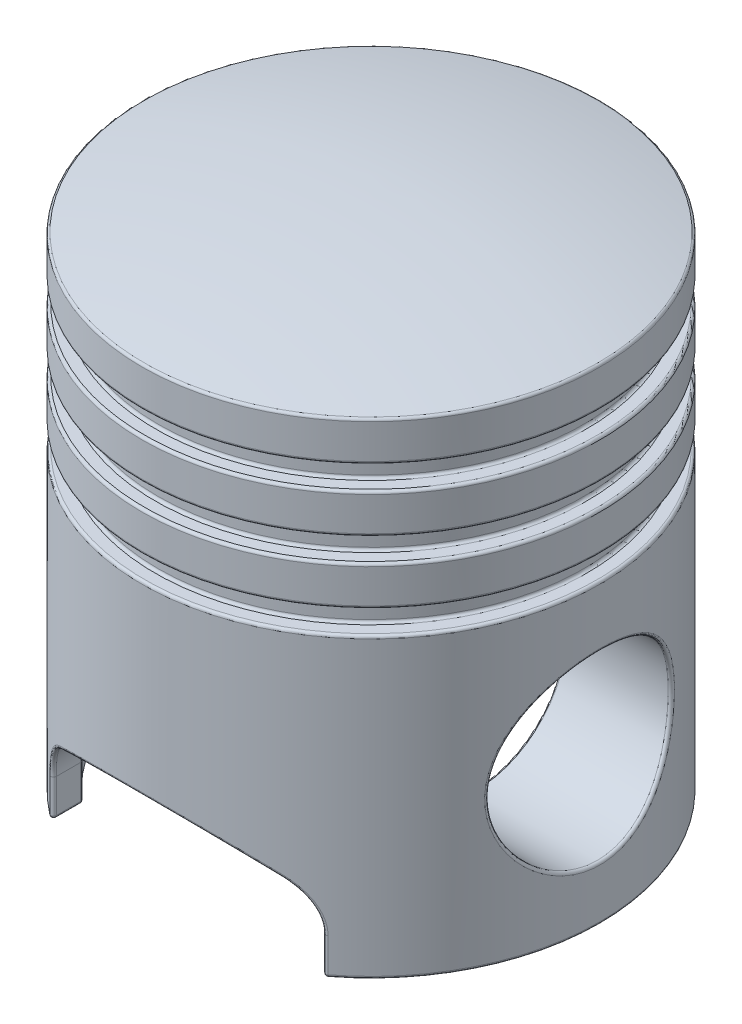
SolidWorks part; units mm, degrees
ref_plane "Front Plane" through (0, 0, 0) normal (0, 0, 1) x (1, 0, 0)
ref_plane "Top Plane" through (0, 0, 0) normal (0, 1, 0) x (1, 0, 0)
ref_plane "Right Plane" through (0, 0, 0) normal (1, 0, 0) x (0, 0, -1)
sketch "Sketch1" plane through (0, 0, 0) normal (0, 0, 1) x (1, 0, 0)
  line L0 (0, 0) -> (0, -76008.205) construction
  line L1 (0, 0) -> (76008.205, 0) construction
  line L2 (0, 95) -> (0, 85)
  line L3 (0, 85) -> (38, 85)
  line L4 (38, 85) -> (38, 0)
  line L5 (38, 0) -> (42.5, 0)
  line L6 (42.5, 0) -> (42.5, 55.2)
  line L7 (42.5, 55.2) -> (39.5, 55.2)
  line L8 (39.5, 55.2) -> (39.5, 59.5)
  line L9 (39.5, 59.5) -> (42.5, 59.5)
  line L10 (42.5, 59.5) -> (42.5, 66.8)
  line L11 (42.5, 66.8) -> (39.5, 66.8)
  line L12 (39.5, 66.8) -> (39.5, 71.1)
  line L13 (39.5, 71.1) -> (42.5, 71.1)
  line L14 (42.5, 71.1) -> (42.5, 78.4)
  line L15 (42.5, 78.4) -> (39.5, 78.4)
  line L16 (39.5, 78.4) -> (39.5, 82.7)
  line L17 (39.5, 82.7) -> (42.5, 82.7)
  line L18 (42.5, 82.7) -> (42.5, 90)
  arc A0 (0, 95) -> (42.5, 90) centre (0, -88.125) cw
  point P7 (0, 0)
  point P24 (5.7863, 67.9402)
  point P26 (61.7259, 86.9589)
  dimension "D1" = 85
  dimension "D2" = 5
  dimension "D3" = 79
  dimension "D4" = 76
  dimension "D5" = 7.3
  dimension "D6" = 4.3
  dimension "D7" = 90
  dimension "D8" = 85
revolve "Revolve1" add sketch "Sketch1" angle 360 about L0
sketch "Sketch2" plane through (0, 0, 0) normal (1, 0, 0) x (0, 0, -1)
  circle A0 centre (0, 27) radius 22.5
  dimension "D1" = 45
  dimension "D2" = 27
extrude "Boss-Extrude1" add sketch "Sketch2" along normal up to next from offset 19
mirror "Mirror1" about plane through (0, 0, 0) normal (1, 0, 0) of "Boss-Extrude1"
sketch "Sketch3" plane through (0, 0, 0) normal (1, 0, 0) x (0, 0, -1)
  circle A0 centre (0, 27) radius 16.9
  dimension "D2" = 33.8
  dimension "D1" = 27
extrude "Cut-Extrude1" cut sketch "Sketch3" against normal through all both and the other way through all
sketch "Sketch4" plane through (0, 0, 0) normal (0, 0, 1) x (1, 0, 0)
  line L0 (0, 0) -> (0, -50000) construction
  line L1 (-25, 0) -> (-25, 12)
  line L2 (-42.5, 0) -> (42.5, 0) construction
  line L3 (25, 0) -> (25, 12)
  line L4 (-25, 0) -> (25, 0)
  arc A0 (-25, 12) -> (25, 12) centre (0, -19.225) cw
  point P10 (0, 0)
  dimension "D2" = 40
  dimension "D1" = 50
  dimension "D3" = 12
extrude "Cut-Extrude2" cut sketch "Sketch4" against normal blind 30 from offset 25 offset against normal yes
fillet "Fillet1" radius 10 2 edges at (25, 12, -31.4937) (-25, 12, -31.4937)
mirror "Mirror2" about plane through (0, 0, 0) normal (0, 0, 1) of "Cut-Extrude2", "Fillet1"
fillet "Fillet2" radius 0.5 50 edges at (-23.3798, 12.2128, 35.4913) (-24.3258, 10.3653, 29.1934) (22.703, 13.1326, 35.928) (23.5198, 11.9916, 29.8466) (3.5136, 20.6204, 42.3545) (25, 0, 31.4937) (-25, 0, 31.4937) (-22.703, 13.1326, -35.928) (-23.5198, 11.9916, -29.8466) (23.3798, 12.2128, -35.4913) (24.3258, 10.3653, -29.1934) (3.5136, 20.6204, -42.3545) (-25, 0, -31.4937) (25, 0, -31.4937) (30.6228, 26.906, -22.4998) (0, 90, 42.5) (0, 82.7, 42.5) (0, 82.7, 39.5) (0, 78.4, 39.5) (0, 78.4, 42.5) (0, 71.1, 42.5) (0, 71.1, 39.5) (0, 66.8, 39.5) (0, 66.8, 42.5) (0, 59.5, 42.5) (0, 59.5, 39.5) (0, 55.2, 39.5) (0, 55.2, 42.5) (-42.5, 0, 0) (42.5, 0, 0) (-38, 0, 0) (38, 0, 0) (0, 85, 38) (19, 27, -22.5) (-19, 27, -22.5) (-30.6228, 26.906, 22.4998) (39.0756, 29.5019, 16.7138) (-42.4284, 10.2809, -2.4664) (19, 27, -16.9) (-19, 27, 16.9) (3.9775, 20.5768, -37.7913) (-25, 3.3779, -28.6182) (-25, 3.3779, -34.3693) (25, 3.3779, -28.6182) (25, 3.3779, -34.3693) (3.9775, 20.5768, 37.7913) (25, 3.3779, 28.6182) (25, 3.3779, 34.3693) (-25, 3.3779, 28.6182) (-25, 3.3779, 34.3693)
